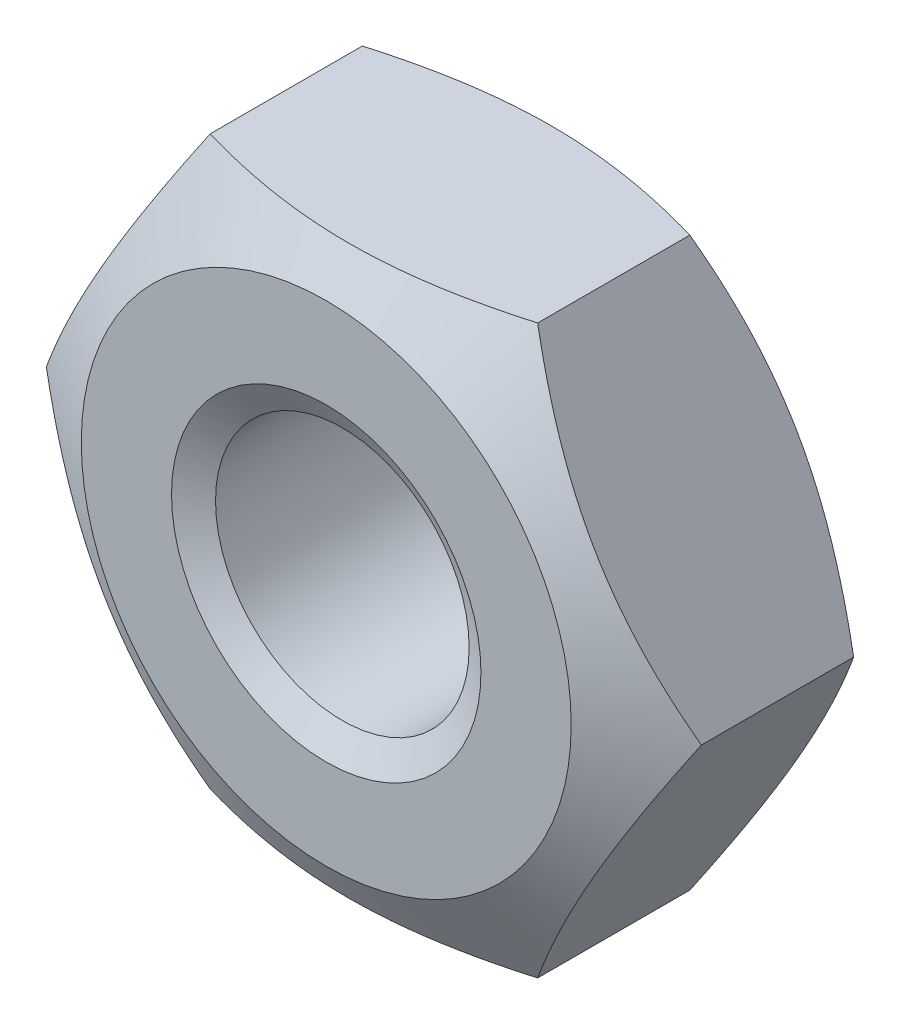
SolidWorks part; units mm, degrees
ref_plane "Front" through (0, 0, 0) normal (0, 0, 1) x (1, 0, 0)
ref_plane "Top" through (0, 0, 0) normal (0, 1, 0) x (1, 0, 0)
ref_plane "Right" through (0, 0, 0) normal (1, 0, 0) x (0, 0, -1)
sketch "Sketch1" plane through (0, 0, 0) normal (0, 0, 1) x (1, 0, 0)
  line L1 (3.1754, 0) -> (1.5877, 2.75)
  line L2 (1.5877, 2.75) -> (-1.5877, 2.75)
  line L3 (-1.5877, 2.75) -> (-3.1754, 0)
  line L4 (-3.1754, 0) -> (-1.5877, -2.75)
  line L5 (-1.5877, -2.75) -> (1.5877, -2.75)
  line L6 (1.5877, -2.75) -> (3.1754, 0)
  circle A0 centre (0, 0) radius 2.75 construction
  circle A1 centre (0, 0) radius 1.2295
  dimension "D" = 2.459
  dimension "s" = 5.5
extrude "BaseNut" add sketch "Sketch1" against normal blind 2.4
sketch "Sketch2" plane through (0, 0, 0) normal (0, 1, 0) x (1, 0, 0)
  line L0 (-3.1754, 2.4) -> (-2.375, 2.4)
  line L2 (-2.375, 2.4) -> (-3.1754, 1.9379)
  line L3 (-3.1754, 1.9379) -> (-3.1754, 2.4)
  line L4 (0, 3.3759) -> (0, -9.8171) construction
  line L6 (-9.7712, 1.2) -> (9.8853, 1.2) construction
  line L7 (-3.1754, 0.4621) -> (-3.1754, 0)
  line L8 (-2.375, 0) -> (-3.1754, 0.4621)
  line L9 (-3.1754, 0) -> (-2.375, 0)
  dimension "D1" = 30
  dimension "dw" = 4.75
  dimension "D2" = 1.2
revolve "Double-Chamfer" cut sketch "Sketch2" angle 360 about L4
chamfer "EndChamfer" distance 0.2705 angle 30 2 edges at (1.2295, 0, -2.4) (1.2295, 0, 0)
sketch "Sketch3" plane through (0, 0, 0) normal (0, 1, 0) x (1, 0, 0)
  line L0 (-1.4638, 2.1295) -> (-1.2295, 1.9942)
  line L1 (-1.2295, 1.9942) -> (-0.959, 1.9942)
  line L2 (-0.959, 1.9942) -> (-0.959, 2.2647)
  line L3 (-0.959, 2.2647) -> (-1.2295, 2.2647)
  line L4 (-1.2295, 2.2647) -> (-1.4638, 2.1295)
  line L5 (0, 7.4383) -> (0, 16.8806) construction
  dimension "D1" = 0.2705
  dimension "D2" = 2.459
revolve "Cut-Revolve10" [suppressed] cut sketch "Sketch3" angle 360 about L5
pattern_linear "LPattern10" [suppressed] count 7 spacing 0.3246 along (0, 0, -1)
equation "\"dw@Sketch2\" = \"s@Sketch1\"-0.75"
equation "\"D2@Sketch2\" = \"m@BaseNut\" / 2"
equation "\"D2@Sketch3\" = \"D@Sketch1\""
equation "\"D3@LPattern10\" = \"D1@Sketch3\" * 1.2"
equation "\"D1@LPattern10\" = \"m@BaseNut\"/\"D3@LPattern10\""
